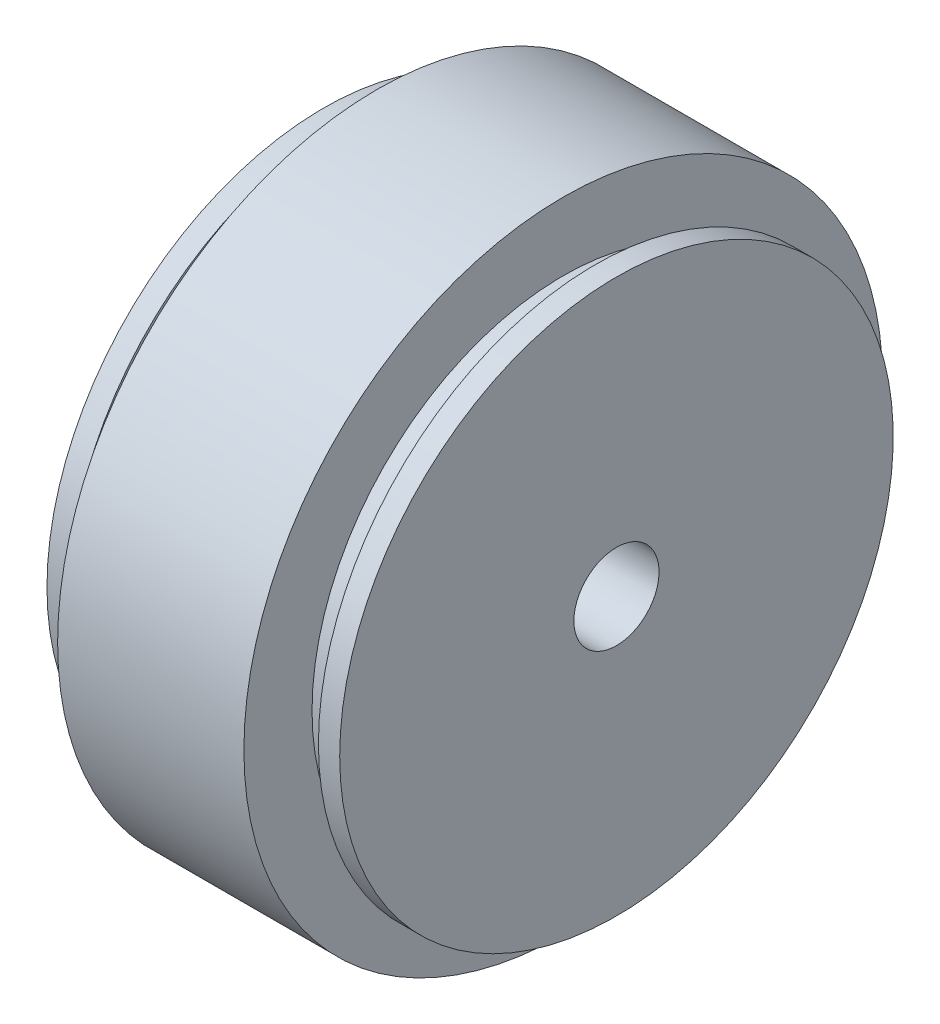
SolidWorks part; units mm, degrees
ref_plane "Plan de face" through (0, 0, 0) normal (0, 0, 1) x (1, 0, 0)
ref_plane "Plan de dessus" through (0, 0, 0) normal (0, 1, 0) x (1, 0, 0)
ref_plane "Plan de droite" through (0, 0, 0) normal (1, 0, 0) x (0, 0, -1)
sketch "Esquisse1" plane through (0, 0, 0) normal (0, 0, 1) x (1, 0, 0)
  line L0 (-2.5, 19.6) -> (-2.5, 26)
  line L1 (2.5, 30) -> (20, 30)
  line L2 (-0.5, 23.6) -> (2.5, 23.6)
  line L3 (0, 23.6) -> (20, 23.6) construction
  line L4 (-0.5, 23.6) -> (-0.5, 26)
  line L5 (25, 26) -> (23, 26)
  line L7 (-2.5, 26) -> (-0.5, 26)
  line L8 (23, 23.6) -> (23, 26)
  line L9 (23, 23.6) -> (20, 23.6)
  line L10 (-2.5, -1.9975) -> (-2.5, 33.1761) construction
  line L11 (-0.5, -1.9975) -> (-0.5, 33.1761) construction
  line L12 (20, 23.6) -> (20, 30)
  line L13 (0, 30) -> (20, 30) construction
  line L14 (2.5, 23.6) -> (2.5, 30)
  line L15 (10, 4) -> (10, 19.6)
  line L16 (25, 4) -> (25, 26)
  line L17 (10, 0) -> (26.9465, 0) construction
  line L18 (10, -1.9975) -> (10, 26) construction
  line L19 (25, -1.9975) -> (25, 26) construction
  line L20 (10, 4) -> (25, 4)
  line L21 (-2.5, 19.6) -> (10, 19.6)
  line L22 (-0.5, 19.6) -> (2.5, 19.6) construction
  line L23 (10, 4) -> (26.9465, 4) construction
revolve "Révolution1" add sketch "Esquisse1" angle 360 about L17
